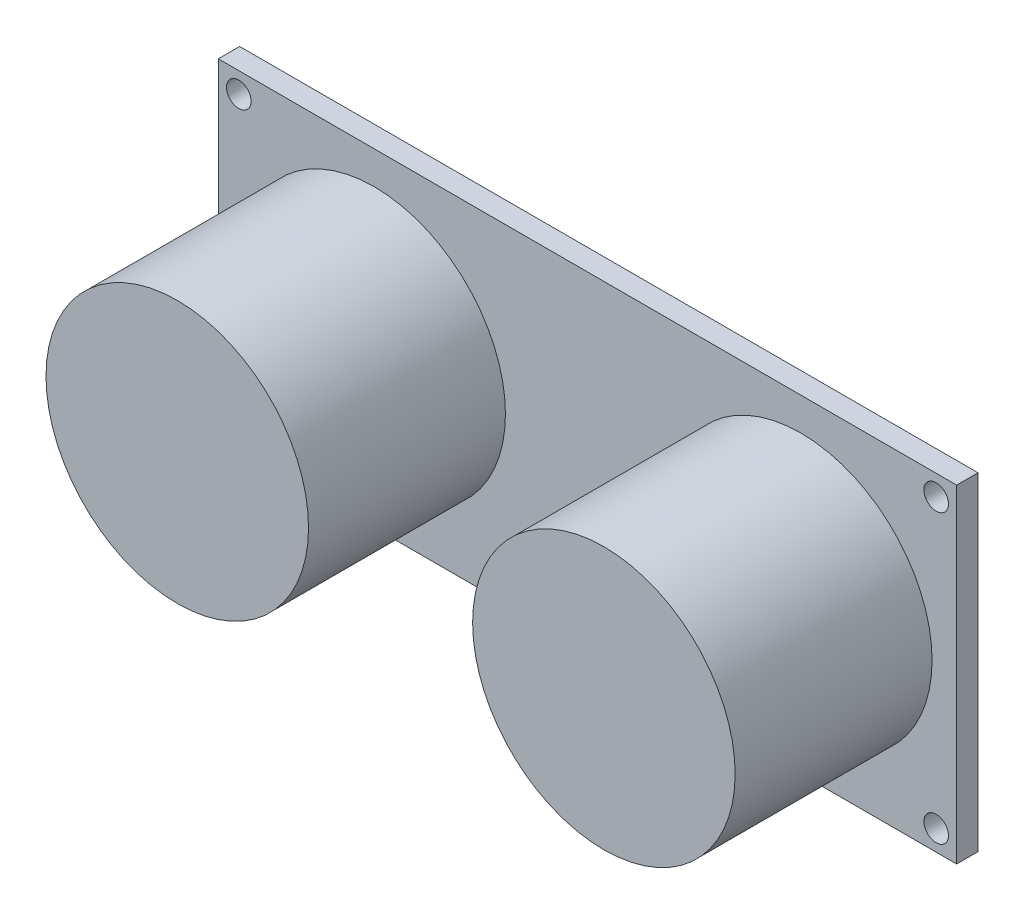
SolidWorks part; units mm, degrees
ref_plane "前视基准面" through (0, 0, 0) normal (0, 0, 1) x (1, 0, 0)
ref_plane "上视基准面" through (0, 0, 0) normal (0, 1, 0) x (1, 0, 0)
ref_plane "右视基准面" through (0, 0, 0) normal (1, 0, 0) x (0, 0, -1)
sketch "草图1" plane through (0, 0, 0) normal (0, 0, 1) x (1, 0, 0)
  line L1 (-22.5, 10) -> (22.5, 10)
  line L2 (-22.5, 10) -> (-22.5, -10)
  line L3 (-22.5, -10) -> (22.5, -10)
  line L4 (22.5, 10) -> (22.5, -10)
  line L5 (0, -10) -> (0, 10) construction
  line L6 (-22.5, 0) -> (22.5, 0) construction
  circle A0 centre (-21.25, 8.75) radius 0.75
  circle A1 centre (21.25, 8.75) radius 0.75
  circle A2 centre (21.25, -8.75) radius 0.75
  circle A3 centre (-21.25, -8.75) radius 0.75
  point P0 (0, 0)
  dimension "D3" = 41
  dimension "D4" = 1.5
  dimension "D5" = 16
  dimension "D1" = 45
  dimension "D2" = 20
extrude "凸台-拉伸1" add sketch "草图1" along normal blind 1.3
sketch "草图2" plane through (0, 0, 1.3) normal (0, 0, 1) x (1, 0, 0)
  line L0 (0, 0) -> (0, 13.5715) construction
  circle A0 centre (-13, 0) radius 8
  circle A1 centre (13, 0) radius 8
  dimension "D1" = 16
  dimension "D2" = 26
extrude "凸台-拉伸2" add sketch "草图2" along normal blind 12
sketch "草图3" plane through (0, 0, 0) normal (0, 0, -1) x (-1, 0, 0)
  line L0 (22.5, -10) -> (-22.5, -10) construction
  line L2 (2.5, -10) -> (5, -10)
  line L3 (2.5, -10) -> (2.5, -7.5)
  line L4 (2.5, -7.5) -> (5, -7.5)
  line L5 (5, -10) -> (5, -7.5)
  dimension "D1" = 2.5
  dimension "D2" = 5
extrude "凸台-拉伸3" add sketch "草图3" along normal blind 2.5
ref_plane "基准面4" through (-3.75, 0, 0) normal (-1, 0, 0) x (0, 0, 1)
sketch "草图4" plane through (-3.75, 0, 0) normal (-1, 0, 0) x (0, 0, 1)
  line L0 (-2.5, -10) -> (-2.5, -7.5) construction
  line L1 (-2.5, -10) -> (-2.5, -7.5) construction
  line L2 (-2.5, -8.75) -> (-3.2, -8.75)
  line L3 (-3.7, -9.25) -> (-3.7, -16.45)
  arc A0 (-3.2, -8.75) -> (-3.7, -9.25) centre (-3.2, -9.25) ccw
  dimension "D3" = 0.5
  dimension "D1" = 1.2
  dimension "D2" = 7.7
sketch "草图5" plane through (0, 0, -2.5) normal (0, 0, -1) x (-1, 0, 0)
  line L1 (3.45, -8.45) -> (4.05, -8.45)
  line L2 (3.45, -8.45) -> (3.45, -9.05)
  line L3 (3.45, -9.05) -> (4.05, -9.05)
  line L4 (4.05, -8.45) -> (4.05, -9.05)
  line L5 (3.75, -9.05) -> (3.75, -8.45) construction
  line L6 (3.45, -8.75) -> (4.05, -8.75) construction
  point P0 (3.75, -8.75)
  dimension "D1" = 0.6
sweep "扫描1" add profiles "草图5" path "草图4"
pattern_linear "阵列(线性)3" count 4 spacing 2.54 along (1, 0, 0) of "凸台-拉伸3", "扫描1"
